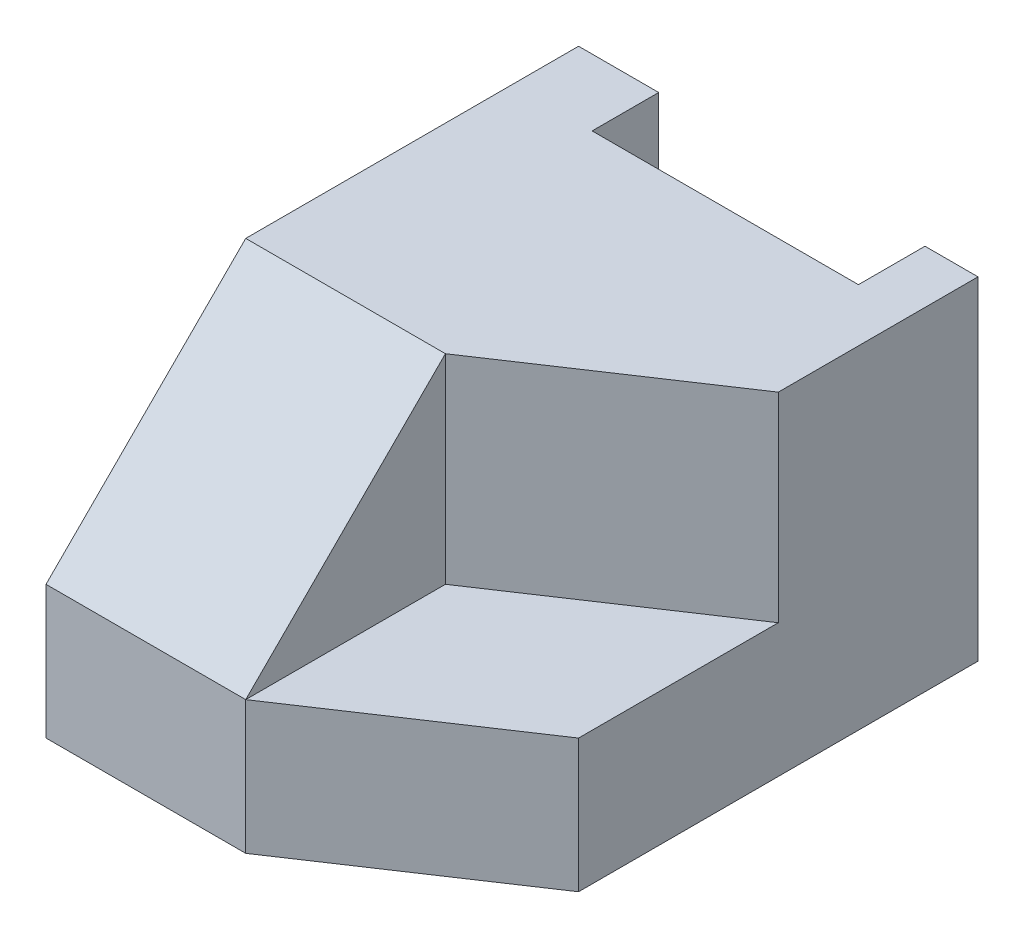
SolidWorks part; units mm, degrees
ref_plane "Front Plane" through (0, 0, 0) normal (0, 0, 1) x (1, 0, 0)
ref_plane "Top Plane" through (0, 0, 0) normal (0, 1, 0) x (1, 0, 0)
ref_plane "Right Plane" through (0, 0, 0) normal (1, 0, 0) x (0, 0, -1)
sketch "Sketch1" plane through (0, 0, 0) normal (0, 1, 0) x (1, 0, 0)
  line L1 (-30, -40) -> (30, -40)
  line L2 (-30, -40) -> (-30, 40)
  line L3 (-30, 40) -> (30, 40)
  line L4 (30, -40) -> (30, 40)
  line L5 (-30, -40) -> (30, 40) construction
  line L6 (-30, 40) -> (30, -40) construction
  point P0 (0, 0)
  dimension "D1" = 60
  dimension "D2" = 80
extrude "Boss-Extrude1" add sketch "Sketch1" along normal blind 50
sketch "Sketch2" plane through (0, 50, 0) normal (0, 1, 0) x (1, 0, 0)
  line L0 (30, 40) -> (-30, 40) construction
  line L1 (22.0372, 40) -> (-17.9628, 40)
  line L2 (22.0372, 40) -> (22.0372, 30)
  line L3 (22.0372, 30) -> (-17.9628, 30)
  line L4 (-17.9628, 40) -> (-17.9628, 30)
  line L5 (30, -40) -> (30, 40) construction
  dimension "D1" = 10
  dimension "D2" = 40
  dimension "D3" = 7.9628
extrude "Cut-Extrude1" cut sketch "Sketch2" against normal blind 50
sketch "Sketch3" plane through (0, 50, 0) normal (0, 1, 0) x (1, 0, 0)
  line L0 (30, -40) -> (30, 40) construction
  line L1 (-30, -40) -> (30, -40) construction
  line L2 (0, -10) -> (30, 10)
  line L3 (30, 10) -> (30, -40)
  line L4 (30, -40) -> (0, -40)
  line L5 (0, -40) -> (0, -10)
  point P0 (30, 10)
  point P1 (0, -10)
  point P4 (0, -40)
  dimension "D1" = 30
  dimension "D2" = 30
  dimension "D3" = 50
  dimension "D4" = 30
extrude "Cut-Extrude2" cut sketch "Sketch3" against normal blind 30
sketch "Sketch4" plane through (0, 20, 0) normal (0, 1, 0) x (1, 0, 0)
  line L0 (0, -40) -> (30, -20)
  line L1 (0, -40) -> (30, -40) construction
  line L2 (0, -10) -> (0, -40) construction
  line L3 (30, -40) -> (30, 10) construction
  line L4 (30, -20) -> (30, -40)
  line L5 (30, -40) -> (0, -40)
  dimension "D1" = 20
extrude "Cut-Extrude3" cut sketch "Sketch4" against normal blind 30
chamfer "Chamfer1" distance 30 angle 45 1 edges at (-15, 50, 40)
